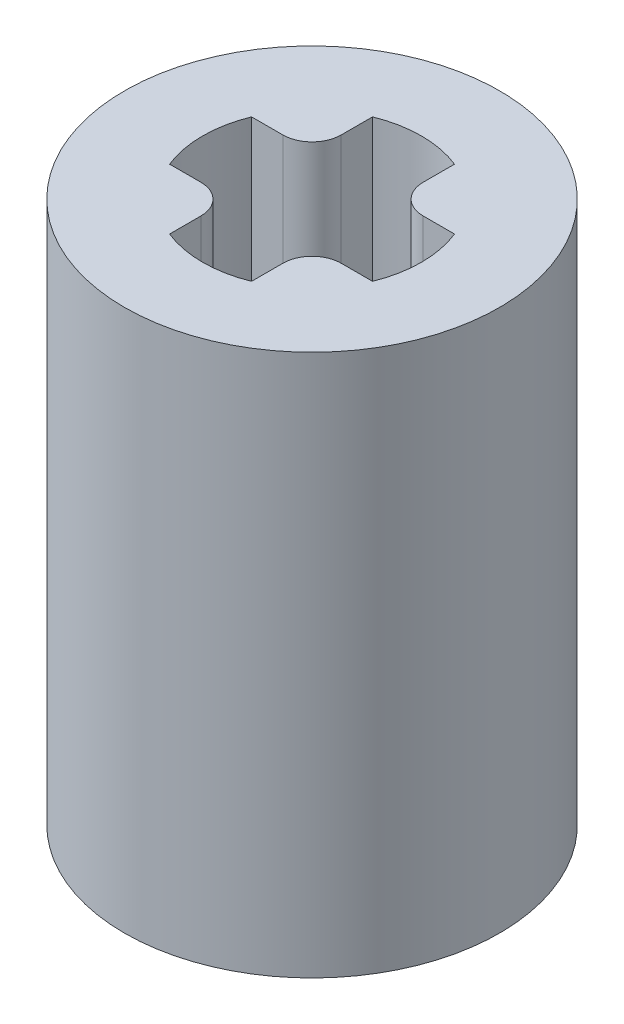
SolidWorks part; units mm, degrees
ref_plane "Front Plane" through (0, 0, 0) normal (0, 0, 1) x (1, 0, 0)
ref_plane "Top Plane" through (0, 0, 0) normal (0, 1, 0) x (1, 0, 0)
ref_plane "Right Plane" through (0, 0, 0) normal (1, 0, 0) x (0, 0, -1)
sketch "Sketch1" plane through (0, 0, 0) normal (0, 1, 0) x (1, 0, 0)
  circle A0 centre (0, 0) radius 4.5
  dimension "D1" = 9
extrude "Boss-Extrude1" add sketch "Sketch1" along normal mid plane 13
sketch "Sketch2" plane through (0, -6.5, 0) normal (0, -1, 0) x (1, 0, 0)
  line L0 (-1.5865, -2.1151) -> (-1.5865, 2.1151)
  line L1 (1.5865, 2.1151) -> (1.5865, -2.1151)
  arc A0 (-1.5865, -2.1151) -> (1.5865, -2.1151) centre (0, 0) ccw
  arc A1 (1.5865, 2.1151) -> (-1.5865, 2.1151) centre (0, 0) ccw
  dimension "D1" = 5.288
  dimension "D2" = 3.173
extrude "Cut-Extrude1" cut sketch "Sketch2" against normal blind 6
sketch "Sketch3" plane through (0, 6.5, 0) normal (0, 1, 0) x (1, 0, 0)
  line L0 (0, 2.625) -> (0, -2.625) construction
  line L1 (-2.625, 0) -> (2.625, 0) construction
  line L2 (0.983, 2.434) -> (0.983, 1.683)
  line L3 (1.683, 0.983) -> (2.434, 0.983)
  line L4 (-0.983, 2.434) -> (-0.983, 1.683)
  line L5 (-1.683, 0.983) -> (-2.434, 0.983)
  line L6 (-1.683, -0.983) -> (-2.434, -0.983)
  line L7 (-0.983, -2.434) -> (-0.983, -1.683)
  line L8 (0.983, -2.434) -> (0.983, -1.683)
  line L9 (1.683, -0.983) -> (2.434, -0.983)
  arc A0 (-2.434, 0.983) -> (-2.434, -0.983) centre (0, 0) ccw
  arc A1 (0.983, 1.683) -> (1.683, 0.983) centre (1.683, 1.683) ccw
  arc A2 (-0.983, 1.683) -> (-1.683, 0.983) centre (-1.683, 1.683) cw
  arc A3 (-0.983, -1.683) -> (-1.683, -0.983) centre (-1.683, -1.683) ccw
  arc A4 (0.983, -1.683) -> (1.683, -0.983) centre (1.683, -1.683) cw
  arc A5 (0.983, 2.434) -> (-0.983, 2.434) centre (0, 0) ccw
  arc A6 (2.434, -0.983) -> (2.434, 0.983) centre (0, 0) ccw
  arc A7 (-0.983, -2.434) -> (0.983, -2.434) centre (0, 0) ccw
  dimension "D1" = 5.25
  dimension "D3" = 0.7
  dimension "D2" = 1.966
extrude "Cut-Extrude2" cut sketch "Sketch3" against normal blind 6
